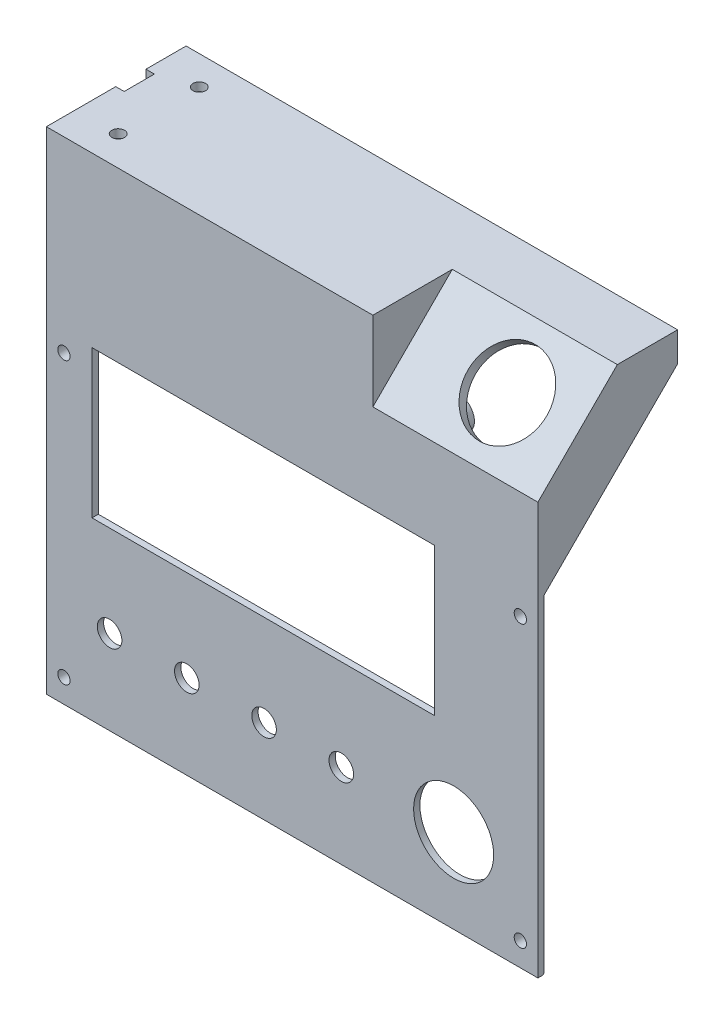
SolidWorks part; units mm, degrees
material "ABS"
ref_plane "Front" through (0, 0, 0) normal (0, 0, 1) x (1, 0, 0)
ref_plane "Top" through (0, 0, 0) normal (0, 1, 0) x (1, 0, 0)
ref_plane "Right" through (0, 0, 0) normal (1, 0, 0) x (0, 0, -1)
sketch "Croquis1" plane through (0, 0, 0) normal (0, 0, 1) x (1, 0, 0)
  line L1 (70, -70) -> (-70, -70)
  line L2 (70, -70) -> (70, 70)
  line L3 (70, 70) -> (-70, 70)
  line L4 (-70, -70) -> (-70, 70)
  line L5 (70, -70) -> (-70, 70) construction
  line L6 (70, 70) -> (-70, -70) construction
  point P0 (0, 0)
  dimension "D1" = 140
  dimension "D2" = 140
extrude "FRENTE" add sketch "Croquis1" along normal blind 1.8
sketch "Croquis32" plane through (0, 0, 0) normal (0, 0, -1) x (-1, 0, 0)
  line L0 (66, 66) -> (-66, 66)
  line L1 (67.6, -67.6) -> (-67.6, -67.6)
  line L2 (67.6, -67.6) -> (67.6, 67.6)
  line L3 (67.6, 67.6) -> (-67.6, 67.6)
  line L4 (-67.6, -67.6) -> (-67.6, 67.6)
  line L5 (67.6, -67.6) -> (-67.6, 67.6) construction
  line L6 (67.6, 67.6) -> (-67.6, -67.6) construction
  line L7 (-66, -66) -> (-66, 66)
  line L8 (66, -66) -> (-66, -66)
  line L9 (66, -66) -> (66, 66)
  line L10 (-70, -70) -> (-70, 70) construction
  line L11 (-70, 70) -> (70, 70) construction
  point P0 (0, 0)
  dimension "D2" = 2.4
  dimension "D3" = 2.4
  dimension "D1" = 1.6
extrude "Saliente-Extruir5" add sketch "Croquis32" along normal blind 2.1
sketch "Croquis33" plane through (0, 0, 0) normal (0, 0, -1) x (-1, 0, 0)
  line L0 (-70, -70) -> (-70, 70) construction
  line L1 (70, -70) -> (-70, -70) construction
  line L2 (-67.6, -60.2603) -> (-67.6, -66.3397)
  line L3 (-67.6, 67.6) -> (-67.6, -67.6) construction
  arc A0 (-67.6, -66.3397) -> (-67.6, -60.2603) centre (-65, -63.3) ccw
  dimension "D1" = 5
  dimension "D2" = 8
  dimension "D3" = 6.7
extrude "Saliente-Extruir6" add sketch "Croquis33" along normal up to surface (2.1 mm away) up to face at (0, 0, -2.1)
sketch "Croquis29" plane through (0, 0, 0) normal (0, 0, -1) x (-1, 0, 0)
  line L0 (-70, 23.6) -> (-70, 70)
  line L1 (-70, -70) -> (-70, 70) construction
  line L2 (-70, 70) -> (0, 70)
  line L3 (-70, 70) -> (70, 70) construction
  line L4 (-70, 23.6) -> (-67.6, 23.6)
  line L6 (-67.6, 23.6) -> (-67.6, 67.6)
  line L7 (-67.6, 67.6) -> (0, 67.6)
  line L9 (0, 67.6) -> (0, 70)
  line L10 (-67.6, 67.6) -> (-67.6, -67.6) construction
  dimension "D1" = 46.4
extrude "VISERA" add sketch "Croquis29" along normal blind 38
sketch "Croquis30" plane through (70, 0, 0) normal (1, 0, 0) x (0, 0, -1)
  line L0 (0, 23.6) -> (38, 23.6)
  line L1 (38, 23.6) -> (38, 61.6)
  line L2 (38, 70) -> (38, 23.6) construction
  line L3 (38, 61.6) -> (0, 23.6)
  line L4 (0, 23.6) -> (0, -67.6) construction
  dimension "D1" = 45
extrude "Cortar-Extruir1" cut sketch "Croquis30" against normal up to surface (2.4 mm away) up to face at (67.6, 45.6, -20.05)
mirror "Simetría3" about plane through (0, 0, 0) normal (1, 0, 0) of "Cortar-Extruir1", "VISERA"
sketch "Croquis37" plane through (70, 0, 0) normal (1, 0, 0) x (0, 0, -1)
  line L0 (25.0701, 70) -> (-1.8, 43.1299)
  line L1 (-1.8, 70) -> (38, 70) construction
  line L2 (-1.8, -70) -> (-1.8, 70) construction
  line L3 (-1.8, 43.1299) -> (-1.8, 70)
  line L4 (-1.8, 70) -> (25.0701, 70)
  line L5 (38, 61.6) -> (0, 23.6) construction
  dimension "D1" = 38
extrude "Saliente-Extruir9" add sketch "Croquis37" against normal blind 50
sketch "Croquis38" plane through (70, 0, 0) normal (1, 0, 0) x (0, 0, -1)
  line L0 (20.8274, 70) -> (-1.8, 47.3726)
  line L1 (-1.8, 70) -> (25.0701, 70) construction
  line L2 (-1.8, 43.1299) -> (-1.8, 70) construction
  line L3 (-1.8, 47.3726) -> (-1.8, 70)
  line L4 (-1.8, 70) -> (20.8274, 70)
  line L5 (25.0701, 70) -> (-1.8, 43.1299) construction
  dimension "D1" = 3
extrude "Cortar-Extruir4" cut sketch "Croquis38" against normal offset from surface (47 mm away) 3 up to face at (20, 62.426, -5.374)
sketch "Croquis39" plane through (0, 24.5863, 24.5863) normal (0, 0.7071, 0.7071) x (1, 0, 0)
  line L0 (70, 32.2247) -> (70, 64.2247) construction
  circle A0 centre (50, 48.2247) radius 11.25
  point P4 (70, 48.2247)
  dimension "D1" = 22.5
  dimension "D2" = 20
extrude "O-PE" cut sketch "Croquis39" against normal up to next
sketch "Croquis15" plane through (0, 0, 1.8) normal (0, 0, 1) x (1, 0, 0)
  circle A0 centre (65, -63.3) radius 1.75
  arc A2 (66, -59.427) -> (62.0487, -66) centre (65, -63.3) ccw construction
  dimension "D1" = 3.5
extrude "ROSCA" cut sketch "Croquis15" against normal up to next (3.9 mm away)
mirror "Simetría4" about plane through (0, 0, 0) normal (1, 0, 0) of "ROSCA", "Saliente-Extruir6"
pattern_linear "MatrizL1" count 2 spacing 80 along (0, 1, 0) of "Saliente-Extruir6", "ROSCA", "Simetría4"
sketch "Croquis19" plane through (0, 0, 0) normal (0, 0, -1) x (-1, 0, 0)
  line L1 (57, -20) -> (-40.6, -20)
  line L2 (57, -20) -> (57, 22)
  line L3 (57, 22) -> (-40.6, 22)
  line L4 (-40.6, -20) -> (-40.6, 22)
  line L5 (57, -20) -> (-40.6, 22) construction
  line L6 (57, 22) -> (-40.6, -20) construction
  line L7 (66, 20.573) -> (66, 66) construction
  line L8 (-70, 70) -> (70, 70) construction
  point P0 (8.2, 1)
  dimension "D1" = 97.6
  dimension "D2" = 42
  dimension "D3" = 9
  dimension "D4" = 48
extrude "VISTA-DISPLAY" cut sketch "Croquis19" against normal up to next
sketch "Croquis24" plane through (0, 0, 1.8) normal (0, 0, 1) x (1, 0, 0)
  line L0 (-70, -70) -> (70, -70) construction
  line L1 (-70, 70) -> (-70, -70) construction
  circle A5 centre (-52, -46) radius 3.5
  dimension "D1" = 7
  dimension "D2" = 24
  dimension "D3" = 18
extrude "POTENCIOMETROS" cut sketch "Croquis24" against normal up to next (1.8 mm away)
pattern_linear "MatrizL3" count 4 spacing 22 along (1, 0, 0) of "POTENCIOMETROS"
sketch "Croquis36" plane through (0, 0, 0) normal (0, 0, -1) x (-1, 0, 0)
  line L0 (-62.0487, -66) -> (62.0487, -66) construction
  line L1 (-66, 12.827) -> (-66, -59.427) construction
  circle A0 centre (-46, -46) radius 11.4
  dimension "D1" = 22.8
  dimension "D2" = 20
  dimension "D3" = 20
extrude "Cortar-Extruir2" cut sketch "Croquis36" against normal up to next
sketch "SOP-DISP" plane through (0, 0, 0) normal (0, 0, -1) x (-1, 0, 0)
  line L1 (-40.6443, 28.9899) -> (-41.9433, 26.7399)
  line L2 (-41.9433, 26.7399) -> (-39.3452, 26.7399)
  line L3 (-39.3452, 26.7399) -> (-40.6443, 28.9899)
  line L8 (-46.6443, -19.2101) -> (-47.9433, -21.4601)
  line L9 (-47.9433, -21.4601) -> (-45.3452, -21.4601)
  line L10 (-45.3452, -21.4601) -> (-46.6443, -19.2101)
  line L15 (-0.6519, 4.5) -> (-0.6519, -0.1272) construction
  circle A0 centre (-40.6443, 27.4899) radius 1.5 construction
  circle A1 centre (-40.6443, 27.4899) radius 3.9
  circle A4 centre (-46.6443, -20.7101) radius 3.9
  circle A6 centre (-46.6443, -20.7101) radius 1.5 construction
  dimension "D1" = 3
  dimension "D2" = 2.4
  dimension "D5" = 2
extrude "sop-display-tornillo" [suppressed] add sketch "SOP-DISP" along normal blind 22.4
sketch "Croquis27" [suppressed] plane through (0, 0, 0) normal (0, 0, -1) x (-1, 0, 0)
  line L0 (62.6, 37.1839) -> (62.6, -37.1839) construction
  line L1 (62.6, -3.3) -> (-62.6, -3.3)
  line L2 (62.6, -3.3) -> (62.6, 25.5)
  line L3 (62.6, 25.5) -> (-16, 25.5)
  line L4 (-16, -1.3) -> (-16, 25.5)
  line L6 (-14.8, 24.3) -> (58, 24.3)
  line L7 (-14.8, 24.3) -> (-14.8, -1.3)
  line L8 (-14.8, -1.3) -> (58, -1.3)
  line L9 (58, 24.3) -> (58, -1.3)
  line L11 (-16, -1.3) -> (-62.6, -1.3)
  line L12 (-62.6, -37.1839) -> (-62.6, 37.1839) construction
  line L13 (-62.6, -1.3) -> (-62.6, -3.3)
  line L14 (-62.6, 37.1839) -> (-62.6, -37.1839) construction
  dimension "D1" = 1.2
  dimension "D2" = 1.2
  dimension "D3" = 2
extrude "Saliente-Extruir2" [suppressed] add sketch "Croquis27" along normal blind 4
sketch "Croquis2" plane through (2.9724, -26.788, 0) normal (0, 0, -1) x (-1, 0, 0)
  line L0 (-16.1655, 23.7794) -> (-16.1655, 8.4994) construction
  line L2 (35.9045, 56.7594) -> (-16.1655, 56.7594) construction
  line L3 (-16.1655, 56.7594) -> (-16.1655, 51.6794) construction
  line L4 (-16.1655, 56.7594) -> (-46.6455, 56.7594) construction
  line L5 (34.6345, 8.4994) -> (-40.2955, 8.4994) construction
  line L6 (-16.1655, 51.6794) -> (-16.1655, 23.7794) construction
  line L7 (49.8745, 59.2994) -> (-51.7255, 59.2994) construction
  line L8 (49.8745, 59.2994) -> (49.8745, 5.9594) construction
  line L9 (49.8745, 5.9594) -> (-51.7255, 5.9594) construction
  line L10 (-51.7255, 5.9594) -> (-51.7255, 59.2994) construction
  line L11 (49.8745, 26.8994) -> (56.2245, 26.8994) construction
  line L12 (56.2245, 26.8994) -> (56.2245, 12.4994) construction
  line L13 (56.2245, 12.4994) -> (49.8745, 12.4994) construction
  circle A0 centre (35.9045, 56.7594) radius 4
  circle A1 centre (35.9045, 56.7594) radius 1.2
  circle A2 centre (34.6345, 8.4994) radius 4 construction
  circle A3 centre (34.6345, 8.4994) radius 1.2 construction
  circle A4 centre (-16.1655, 51.6794) radius 4
  circle A5 centre (-16.1655, 51.6794) radius 1.2
  circle A6 centre (-46.6455, 56.7594) radius 4 construction
  circle A7 centre (-46.6455, 56.7594) radius 1.2 construction
  circle A8 centre (-40.2955, 8.4994) radius 4 construction
  circle A9 centre (-40.2955, 8.4994) radius 1.2 construction
  circle A10 centre (-16.1655, 23.7794) radius 4
  circle A11 centre (-16.1655, 23.7794) radius 1.2
  dimension "D1" = 8
  dimension "D2" = 2.4
  dimension "D3" = 2.54
  dimension "D4" = 13.97
  dimension "D5" = 15.24
  dimension "D6" = 90.17
  dimension "D7" = 66.04
  dimension "D8" = 96.52
  dimension "D9" = 7.62
  dimension "D10" = 50.8
  dimension "D12" = 27.9
  dimension "D13" = 53.34
  dimension "D14" = 101.6
  dimension "D15" = 32.4
  dimension "D16" = 14.4
  dimension "D17" = 6.35
extrude "Mega-UNO" [suppressed] add sketch "Croquis2" along normal blind 5
other "MONTAJE-ARDUINO-MEGA-UNO_H<1>" [suppressed]
chamfer "Chaflán1" distance 0.4 angle 45 1 edges at (0, -70, 0)
ref_plane "Plano1" through (-12, 0, 0) normal (1, 0, 0) x (0, 0, -1)
sketch "Croquis34" plane through (-12, 0, 0) normal (1, 0, 0) x (0, 0, -1)
  line L0 (0.8058, 67.6) -> (8.6, 63.1)
  line L1 (38, 67.6) -> (2.1, 67.6) construction
  line L2 (8.6, 63.1) -> (9.8, 63.1)
  line L3 (9.8, 63.1) -> (9.8, 64.3)
  line L4 (9.8, 64.3) -> (11.6, 64.3)
  line L5 (11.6, 64.3) -> (11.6, 63.5)
  line L6 (11.6, 63.5) -> (12.5, 63.5)
  line L7 (12.5, 63.5) -> (12.5, 67.6)
  line L8 (12.5, 67.6) -> (0.8058, 67.6)
  line L10 (0, 20.573) -> (0, 66) construction
  dimension "D1" = 9.8
  dimension "D2" = 3.3
  dimension "D3" = 1.2
  dimension "D4" = 0.8
  dimension "D5" = 0.9
  dimension "D6" = 1.2
  dimension "D7" = 30
  dimension "D8" = 1.8
extrude "Saliente-Extruir7" [suppressed] add sketch "Croquis34" against normal blind 5
sketch "Croquis35" [suppressed] plane through (-12, 0, 0) normal (1, 0, 0) x (0, 0, -1)
  line L0 (0, -6.5) -> (12.5, -6.5)
  line L1 (12.5, -6.5) -> (12.5, -3.3)
  line L2 (12.5, -3.3) -> (11.6, -3.3)
  line L3 (11.6, -3.3) -> (11.6, -4.1)
  line L4 (11.6, -4.1) -> (9.8, -4.1)
  line L5 (9.8, -4.1) -> (9.8, -2.9)
  line L6 (9.8, -2.9) -> (8.6, -2.9)
  line L7 (8.6, -2.9) -> (6.5215, -4.1)
  line L8 (6.5215, -4.1) -> (0, -4.1)
  line L9 (0, -4.1) -> (0, -6.5)
  line L10 (0, 14.2913) -> (0, 56) construction
  line L11 (9.8, 53.1) -> (9.8, 54.3) construction
  line L12 (11.6, 54.3) -> (11.6, 53.5) construction
  line L13 (9.8, 54.3) -> (11.6, 54.3) construction
  dimension "D1" = 58.4
  dimension "D2" = 2.4
  dimension "D3" = 30
extrude "Saliente-Extruir8" [suppressed] add sketch "Croquis35" against normal blind 8
pattern_linear "MatrizL2" [suppressed] count 2 spacing 59
fillet "Redondeo8" [suppressed] radius 3
sketch "Croquis40" plane through (0, 70, 0) normal (0, 1, 0) x (1, 0, 0)
  line L0 (-58, 29.75) -> (-58, 6.65) construction
  line L1 (23, -1.8) -> (-70, -1.8) construction
  line L2 (-70, -1.8) -> (-70, 38) construction
  circle A0 centre (-58, 29.75) radius 1.8
  circle A1 centre (-58, 6.65) radius 1.8
  point P4 (-58, 18.2)
  dimension "D1" = 3.6
  dimension "D2" = 23.1
  dimension "D3" = 20
  dimension "D4" = 12
extrude "MPX-MOUNT" cut sketch "Croquis40" against normal up to next
sketch "Croquis41" plane through (-70, 0, 0) normal (-1, 0, 0) x (0, 0, 1)
  line L0 (-26.56, 70) -> (-26.56, 65.74)
  line L1 (1.8, 70) -> (-38, 70) construction
  line L2 (-17.96, 65.74) -> (-17.96, 70)
  line L3 (-17.96, 70) -> (-26.56, 70)
  line L4 (-22.26, 65.74) -> (-29.75, 65.74) construction
  arc A0 (-26.56, 65.74) -> (-17.96, 65.74) centre (-22.26, 65.74) ccw
  circle A1 centre (-14.13, 58.78) radius 4.3
  dimension "D3" = 8.6
  dimension "D1" = 8.13
  dimension "D2" = 6.96
  dimension "D4" = 4.26
  dimension "D5" = 7.49
extrude "MPX-TUBBING" cut sketch "Croquis41" against normal up to surface (2.4 mm away) up to face at (-67.6, 55.625, -20.05)
sketch "Croquis210" plane through (-7.163, 18.1786, 0) normal (0, 0, -1) x (-1, 0, 0)
  line L0 (-7.203, -9.6986) -> (-7.203, -24.9786) construction
  line L1 (62.837, 5.4214) -> (62.837, -87.7786) construction
  line L2 (44.867, 23.2814) -> (-7.203, 23.2814) construction
  line L3 (-7.203, 23.2814) -> (-7.203, 18.2014) construction
  line L4 (-7.203, 23.2814) -> (-37.683, 23.2814) construction
  line L5 (43.597, -24.9786) -> (-31.333, -24.9786) construction
  line L6 (-7.203, 18.2014) -> (-7.203, -9.6986) construction
  line L7 (58.837, 25.8214) -> (-42.763, 25.8214) construction
  line L8 (58.837, 25.8214) -> (58.837, -27.5186) construction
  line L9 (58.837, -27.5186) -> (-42.763, -27.5186) construction
  line L10 (-42.763, -27.5186) -> (-42.763, 25.8214) construction
  line L11 (58.837, -6.5786) -> (65.187, -6.5786) construction
  line L12 (65.187, -6.5786) -> (65.187, -20.9786) construction
  line L13 (65.187, -20.9786) -> (58.837, -20.9786) construction
  line L14 (62.837, 51.8214) -> (-77.163, 51.8214) construction
  circle A0 centre (44.867, 23.2814) radius 5
  circle A1 centre (44.867, 23.2814) radius 1.2
  circle A2 centre (43.597, -24.9786) radius 5 construction
  circle A3 centre (43.597, -24.9786) radius 1.2 construction
  circle A4 centre (-7.203, 18.2014) radius 5
  circle A5 centre (-7.203, 18.2014) radius 1.2
  circle A6 centre (-37.683, 23.2814) radius 5
  circle A7 centre (-37.683, 23.2814) radius 1.2
  circle A8 centre (-31.333, -24.9786) radius 5 construction
  circle A9 centre (-31.333, -24.9786) radius 1.2 construction
  circle A10 centre (-7.203, -9.6986) radius 5 construction
  circle A11 centre (-7.203, -9.6986) radius 1.2 construction
  dimension "D1" = 10
  dimension "D2" = 2.4
  dimension "D3" = 2.54
  dimension "D4" = 13.97
  dimension "D5" = 15.24
  dimension "D6" = 90.17
  dimension "D7" = 66.04
  dimension "D8" = 96.52
  dimension "D9" = 7.62
  dimension "D10" = 50.8
  dimension "D11" = 4
  dimension "D12" = 27.9
  dimension "D13" = 53.34
  dimension "D14" = 101.6
  dimension "D15" = 32.4
  dimension "D16" = 14.4
  dimension "D17" = 6.35
  dimension "D18" = 26
extrude "Mega-UNO1" add sketch "Croquis210" along normal blind 15 draft 1.5
other "MONTAJE-ARDUINO-MEGA-UNO_H<2>"
